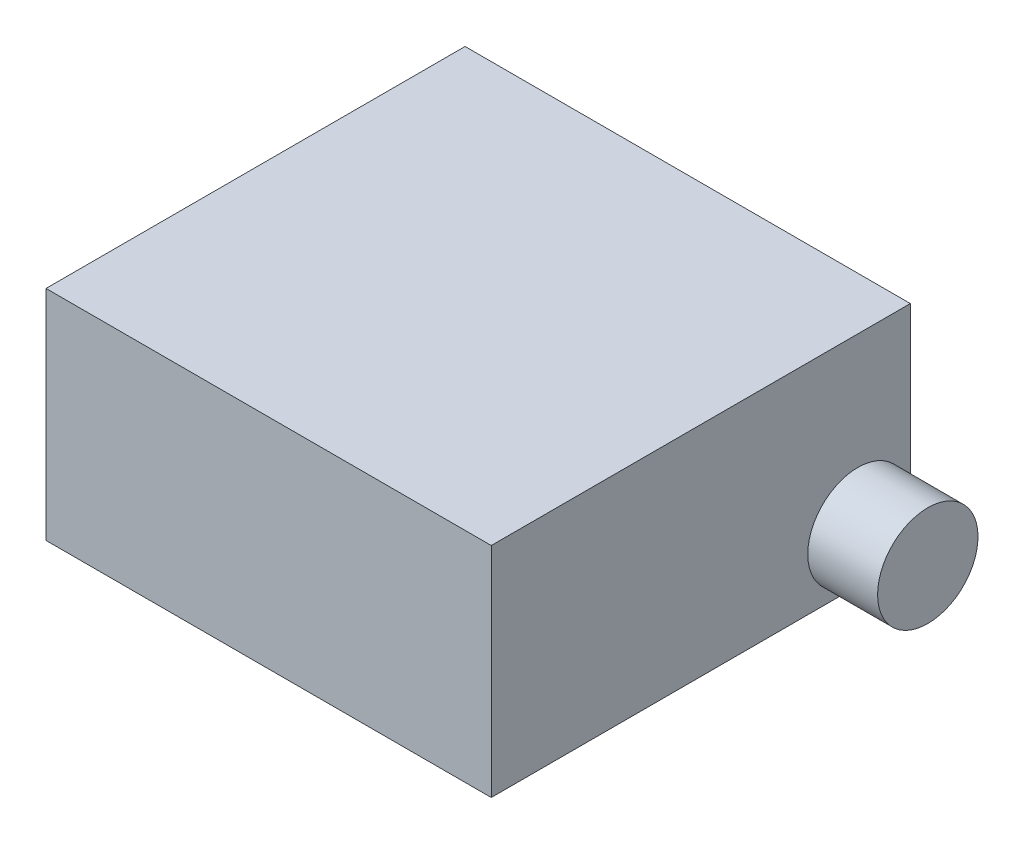
SolidWorks part; units mm, degrees
ref_plane "Front Plane" through (0, 0, 0) normal (0, 0, 1) x (1, 0, 0)
ref_plane "Top Plane" through (0, 0, 0) normal (0, 1, 0) x (1, 0, 0)
ref_plane "Right Plane" through (0, 0, 0) normal (1, 0, 0) x (0, 0, -1)
sketch "Sketch1" plane through (0, 0, 0) normal (0, 1, 0) x (1, 0, 0)
  line L1 (0, 0) -> (10.2, 0)
  line L2 (0, 0) -> (0, 9.6)
  line L3 (0, 9.6) -> (10.2, 9.6)
  line L4 (10.2, 0) -> (10.2, 9.6)
  dimension "D1" = 9.6
  dimension "D2" = 10.2
extrude "Boss-Extrude1" add sketch "Sketch1" along normal blind 5
sketch "Sketch2" plane through (10.2, 0, 0) normal (1, 0, 0) x (0, 0, -1)
  line L0 (0, 0) -> (9.6, 0) construction
  line L1 (9.6, 5) -> (9.6, 0) construction
  circle A0 centre (8.4, 1.2) radius 1.15
  dimension "D1" = 2.3
  dimension "D2" = 1.2
  dimension "D3" = 1.2
extrude "Boss-Extrude2" add sketch "Sketch2" along normal blind 1.6
